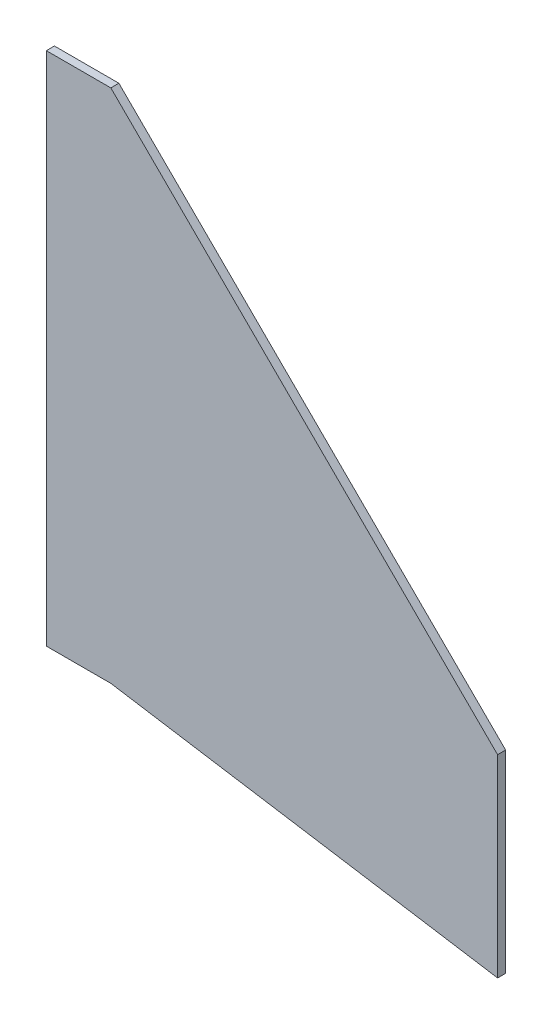
SolidWorks part; units mm, degrees
ref_plane "Front Plane" through (0, 0, 0) normal (0, 0, 1) x (1, 0, 0)
ref_plane "Top Plane" through (0, 0, 0) normal (0, 1, 0) x (1, 0, 0)
ref_plane "Right Plane" through (0, 0, 0) normal (1, 0, 0) x (0, 0, -1)
sketch "Sketch1" plane through (0, 0, 0) normal (0, 0, 1) x (1, 0, 0)
  line L0 (0, 0) -> (0, -203.2)
  line L1 (0, -203.2) -> (152.4, -227.5397)
  line L2 (152.4, -227.5397) -> (152.4, -151.3397)
  line L3 (152.4, -151.3397) -> (0, 0)
  line L4 (0, 0) -> (-25.4, 0)
  line L5 (-25.4, 0) -> (-25.4, -203.2)
  line L6 (-25.4, -203.2) -> (0, -203.2)
  line L7 (0, 0) -> (114.3, 0) construction
  dimension "D1" = 203.2
  dimension "D2" = 76.2
  dimension "D3" = 152.4
  dimension "D4" = 44.8
  dimension "D5" = 25.4
extrude "Boss-Extrude1" add sketch "Sketch1" along normal mid plane 3.175 contours L5 L6 L0 L4 | L2 L3 L0 L1
